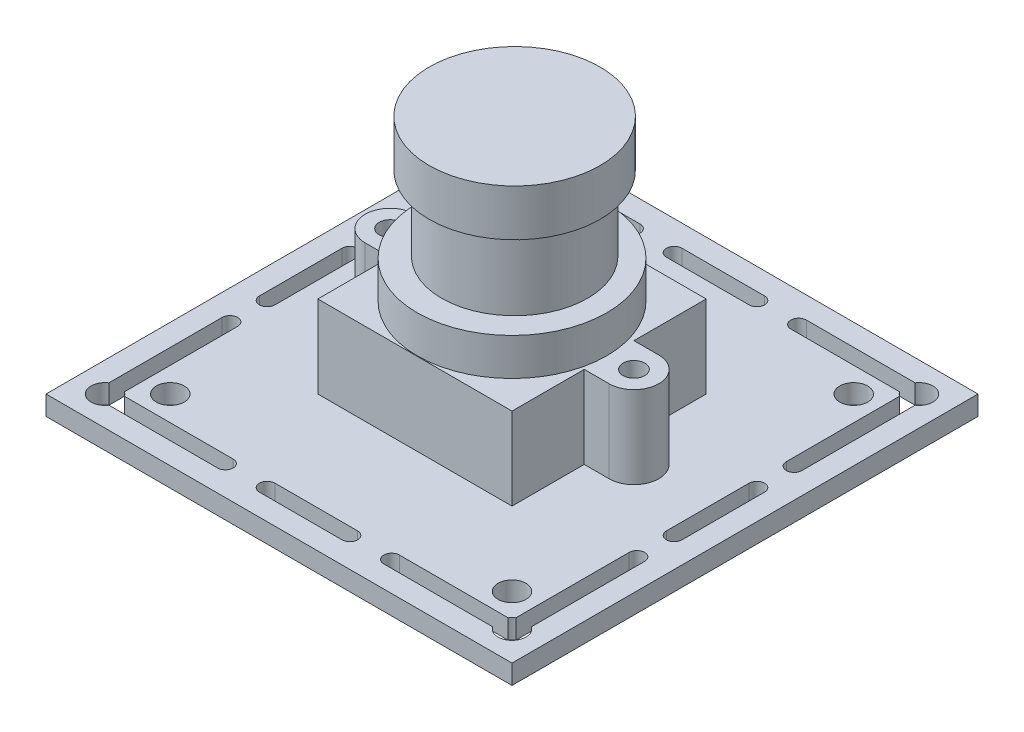
SolidWorks part; units mm, degrees
ref_plane "Front Plane" through (0, 0, 0) normal (0, 0, 1) x (1, 0, 0)
ref_plane "Top Plane" through (0, 0, 0) normal (0, 1, 0) x (1, 0, 0)
ref_plane "Right Plane" through (0, 0, 0) normal (1, 0, 0) x (0, 0, -1)
sketch "Sketch1" plane through (0, 0, 0) normal (0, 1, 0) x (1, 0, 0)
  line L1 (-271.6418, -296.6232) -> (-233.5418, -296.6232)
  line L2 (-271.6418, -296.6232) -> (-271.6418, -334.7232)
  line L3 (-271.6418, -334.7232) -> (-233.5418, -334.7232)
  line L4 (-233.5418, -296.6232) -> (-233.5418, -334.7232)
  line L5 (-271.6418, -296.6232) -> (-233.5418, -334.7232) construction
  line L6 (-271.6418, -334.7232) -> (-233.5418, -296.6232) construction
  point P0 (-252.5918, -315.6732)
  dimension "D1" = 38.1
  dimension "D2" = 38.1
extrude "Boss-Extrude1" add sketch "Sketch1" along normal blind 1.5875
sketch "Sketch4" plane through (0, 1.5875, 0) normal (0, 1, 0) x (1, 0, 0)
  line L0 (-271.6418, -334.7232) -> (-233.5418, -296.6232) construction
  line L1 (-252.5918, -296.6232) -> (-252.5918, -334.7232) construction
  line L2 (-269.2288, -332.3102) -> (-235.9548, -332.3102) construction
  line L3 (-269.2288, -332.3102) -> (-269.2288, -299.0362) construction
  line L4 (-269.8638, -312.295) -> (-269.8638, -319.0514)
  line L5 (-235.9548, -332.3102) -> (-235.9548, -299.0362) construction
  line L6 (-269.2288, -332.3102) -> (-235.9548, -299.0362) construction
  line L7 (-268.4206, -299.8444) -> (-235.9548, -332.3102) construction
  line L8 (-233.5418, -296.6232) -> (-271.6418, -296.6232) construction
  line L9 (-271.6418, -334.7232) -> (-233.5418, -334.7232) construction
  line L10 (-271.6418, -315.6732) -> (-233.5418, -315.6732) construction
  line L11 (-271.6418, -296.6232) -> (-271.6418, -334.7232) construction
  line L12 (-233.5418, -334.7232) -> (-233.5418, -296.6232) construction
  line L13 (-259.3853, -298.4012) -> (-268.2784, -298.4012)
  line L14 (-259.3853, -299.6712) -> (-268.2784, -299.6712)
  line L15 (-255.97, -298.4012) -> (-249.2136, -298.4012)
  line L16 (-255.97, -299.6712) -> (-249.2136, -299.6712)
  line L17 (-255.335, -299.0362) -> (-235.9548, -299.0362) construction
  line L18 (-258.7503, -299.0362) -> (-256.605, -299.0362) construction
  line L19 (-268.5938, -312.295) -> (-268.5938, -319.0514)
  line L20 (-269.2288, -299.6712) -> (-269.2288, -299.0362) construction
  line L21 (-269.8638, -309.247) -> (-269.8638, -299.9865)
  line L22 (-268.5938, -309.247) -> (-268.5938, -299.9865)
  line L23 (-269.2288, -311.66) -> (-269.2288, -309.882) construction
  line L24 (-235.9548, -311.66) -> (-235.9548, -309.882) construction
  line L25 (-235.9548, -299.6712) -> (-235.9548, -299.0362) construction
  line L26 (-246.4333, -299.0362) -> (-248.5786, -299.0362) construction
  line L27 (-236.5898, -309.247) -> (-236.5898, -299.9865)
  line L28 (-235.3198, -309.247) -> (-235.3198, -299.9865)
  line L29 (-236.5898, -312.295) -> (-236.5898, -319.0514)
  line L30 (-245.7983, -299.6712) -> (-236.9052, -299.6712)
  line L31 (-245.7983, -298.4012) -> (-236.9052, -298.4012)
  line L32 (-235.3198, -312.295) -> (-235.3198, -319.0514)
  line L33 (-246.4333, -332.3102) -> (-248.5786, -332.3102) construction
  line L34 (-235.9548, -331.6752) -> (-235.9548, -332.3102) construction
  line L35 (-235.9548, -319.6864) -> (-235.9548, -321.4644) construction
  line L36 (-269.2288, -319.6864) -> (-269.2288, -321.4644) construction
  line L37 (-269.2288, -331.6752) -> (-269.2288, -332.3102) construction
  line L38 (-258.7503, -332.3102) -> (-256.605, -332.3102) construction
  line L39 (-255.335, -332.3102) -> (-235.9548, -332.3102) construction
  line L40 (-268.4206, -331.5019) -> (-235.9548, -299.0362) construction
  line L41 (-269.2288, -299.0362) -> (-235.9548, -332.3102) construction
  line L42 (-271.6418, -296.6232) -> (-233.5418, -334.7232) construction
  line L43 (-245.7983, -332.9452) -> (-236.9052, -332.9452)
  line L44 (-245.7983, -331.6752) -> (-236.9052, -331.6752)
  line L45 (-235.3198, -322.0994) -> (-235.3198, -331.3598)
  line L46 (-236.5898, -322.0994) -> (-236.5898, -331.3598)
  line L47 (-268.5938, -322.0994) -> (-268.5938, -331.3598)
  line L48 (-269.8638, -322.0994) -> (-269.8638, -331.3598)
  line L49 (-255.97, -331.6752) -> (-249.2136, -331.6752)
  line L50 (-255.97, -332.9452) -> (-249.2136, -332.9452)
  line L51 (-259.3853, -331.6752) -> (-268.2784, -331.6752)
  line L52 (-259.3853, -332.9452) -> (-268.2784, -332.9452)
  line L54 (-266.5618, -329.6432) -> (-238.6218, -329.6432) construction
  line L55 (-266.5618, -329.6432) -> (-266.5618, -301.7032) construction
  line L56 (-266.5618, -301.7032) -> (-238.6218, -301.7032) construction
  line L57 (-238.6218, -329.6432) -> (-238.6218, -301.7032) construction
  line L58 (-266.5618, -329.6432) -> (-238.6218, -301.7032) construction
  line L59 (-266.5618, -301.7032) -> (-238.6218, -329.6432) construction
  arc A0 (-255.97, -298.4012) -> (-255.97, -299.6712) centre (-255.97, -299.0362) ccw
  arc A1 (-259.3853, -299.6712) -> (-259.3853, -298.4012) centre (-259.3853, -299.0362) ccw
  arc A2 (-268.2784, -298.4012) -> (-269.8638, -299.9865) centre (-269.2288, -299.0362) ccw
  arc A3 (-268.5938, -312.295) -> (-269.8638, -312.295) centre (-269.2288, -312.295) ccw
  arc A4 (-269.8638, -309.247) -> (-268.5938, -309.247) centre (-269.2288, -309.247) ccw
  arc A5 (-268.5938, -299.9865) -> (-268.2784, -299.6712) centre (-269.2288, -299.0362) ccw
  arc A6 (-236.5898, -299.9865) -> (-236.9052, -299.6712) centre (-235.9548, -299.0362) cw
  arc A7 (-235.3198, -309.247) -> (-236.5898, -309.247) centre (-235.9548, -309.247) cw
  arc A8 (-236.5898, -312.295) -> (-235.3198, -312.295) centre (-235.9548, -312.295) cw
  arc A9 (-236.9052, -298.4012) -> (-235.3198, -299.9865) centre (-235.9548, -299.0362) cw
  arc A10 (-245.7983, -299.6712) -> (-245.7983, -298.4012) centre (-245.7983, -299.0362) cw
  arc A11 (-249.2136, -298.4012) -> (-249.2136, -299.6712) centre (-249.2136, -299.0362) cw
  arc A12 (-249.2136, -332.9452) -> (-249.2136, -331.6752) centre (-249.2136, -332.3102) ccw
  arc A13 (-245.7983, -331.6752) -> (-245.7983, -332.9452) centre (-245.7983, -332.3102) ccw
  arc A14 (-236.9052, -332.9452) -> (-235.3198, -331.3598) centre (-235.9548, -332.3102) ccw
  arc A15 (-236.5898, -319.0514) -> (-235.3198, -319.0514) centre (-235.9548, -319.0514) ccw
  arc A16 (-235.3198, -322.0994) -> (-236.5898, -322.0994) centre (-235.9548, -322.0994) ccw
  arc A17 (-236.5898, -331.3598) -> (-236.9052, -331.6752) centre (-235.9548, -332.3102) ccw
  arc A18 (-268.5938, -331.3598) -> (-268.2784, -331.6752) centre (-269.2288, -332.3102) cw
  arc A19 (-269.8638, -322.0994) -> (-268.5938, -322.0994) centre (-269.2288, -322.0994) cw
  arc A20 (-268.5938, -319.0514) -> (-269.8638, -319.0514) centre (-269.2288, -319.0514) cw
  arc A21 (-268.2784, -332.9452) -> (-269.8638, -331.3598) centre (-269.2288, -332.3102) cw
  arc A22 (-259.3853, -331.6752) -> (-259.3853, -332.9452) centre (-259.3853, -332.3102) cw
  arc A23 (-255.97, -332.9452) -> (-255.97, -331.6752) centre (-255.97, -332.3102) cw
  circle A24 centre (-266.5618, -301.7032) radius 1.143
  circle A25 centre (-238.6218, -301.7032) radius 1.143
  circle A26 centre (-266.5618, -329.6432) radius 1.143
  circle A27 centre (-238.6218, -329.6432) radius 1.143
  point P4 (-252.5918, -315.6732)
  point P31 (-252.5918, -298.4012)
  point P34 (-236.5898, -315.6732)
  point P42 (-252.5918, -331.6752)
  point P44 (-269.8638, -315.6732)
  point P70 (-268.5938, -315.6732)
  point P71 (-252.5918, -299.6712)
  point P84 (-269.2288, -315.6732)
  point P118 (-235.3198, -315.6732)
  point P119 (-252.5918, -332.9452)
  point P120 (-252.5918, -315.6732)
  dimension "D3" = 1.27
  dimension "D4" = 3.3782
  dimension "D5" = 2.286
  dimension "D7" = 3.3782
  dimension "D8" = 1.27
  dimension "D9" = 3.048
  dimension "D12" = 2.286
  dimension "D1" = 33.274
  dimension "D2" = 33.274
  dimension "D6" = 8.8931
  dimension "D10" = 27.94
  dimension "D11" = 27.94
extrude "Cut-Extrude2" cut sketch "Sketch4" against normal blind 7.874
sketch "Sketch6" plane through (0, 1.5875, 0) normal (0, 1, 0) x (1, 0, 0)
  line L0 (-271.6418, -296.6232) -> (-233.5418, -334.7232) construction
  line L2 (-260.5293, -323.6107) -> (-244.6543, -323.6107)
  line L3 (-260.5293, -323.6107) -> (-260.5293, -307.7357)
  line L4 (-260.5293, -307.7357) -> (-244.6543, -307.7357)
  line L5 (-244.6543, -323.6107) -> (-244.6543, -307.7357)
  line L6 (-260.5293, -323.6107) -> (-244.6543, -307.7357) construction
  line L7 (-260.5293, -307.7357) -> (-244.6543, -323.6107) construction
  point P4 (-252.5918, -315.6732)
  dimension "D1" = 15.875
extrude "Boss-Extrude2" add sketch "Sketch6" along normal blind 6.731
sketch "Sketch7" plane through (0, 1.5875, 0) normal (0, 1, 0) x (1, 0, 0)
  line L0 (-242.6223, -313.6412) -> (-244.6543, -313.6412)
  line L1 (-244.6543, -313.6412) -> (-244.6543, -317.7052)
  line L2 (-244.6543, -323.6107) -> (-244.6543, -307.7357) construction
  line L3 (-242.6223, -317.7052) -> (-244.6543, -317.7052)
  line L4 (-252.5918, -296.6232) -> (-252.5918, -334.7232) construction
  line L5 (-233.5418, -296.6232) -> (-271.6418, -296.6232) construction
  line L6 (-271.6418, -334.7232) -> (-233.5418, -334.7232) construction
  line L7 (-262.5613, -317.7052) -> (-260.5293, -317.7052)
  line L8 (-260.5293, -313.6412) -> (-260.5293, -317.7052)
  line L9 (-262.5613, -313.6412) -> (-260.5293, -313.6412)
  arc A0 (-242.6223, -317.7052) -> (-242.6223, -313.6412) centre (-242.6223, -315.6732) ccw
  circle A1 centre (-242.6223, -315.6732) radius 0.889
  circle A2 centre (-262.5613, -315.6732) radius 0.889
  arc A3 (-262.5613, -317.7052) -> (-262.5613, -313.6412) centre (-262.5613, -315.6732) cw
  dimension "D3" = 4.064
  dimension "D1" = 1.778
extrude "Boss-Extrude3" add sketch "Sketch7" along normal blind 6.731
sketch "Sketch8" plane through (0, 8.3185, 0) normal (0, 1, 0) x (1, 0, 0)
  line L0 (-260.5293, -307.7357) -> (-244.6543, -323.6107) construction
  line L1 (-244.6543, -307.7357) -> (-260.5293, -307.7357) construction
  circle A0 centre (-252.4364, -315.8286) radius 7.747
  dimension "D1" = 15.494
extrude "Boss-Extrude4" add sketch "Sketch8" along normal blind 3.048
sketch "Sketch9" plane through (0, 11.3665, 0) normal (0, 1, 0) x (1, 0, 0)
  circle A0 centre (-252.4654, -315.5831) radius 5.969
  dimension "D1" = 11.938
extrude "Boss-Extrude5" add sketch "Sketch9" along normal blind 6.096
sketch "Sketch10" plane through (0, 17.4625, 0) normal (0, 1, 0) x (1, 0, 0)
  circle A0 centre (-252.4654, -315.5831) radius 6.985
  dimension "D1" = 13.97
extrude "Boss-Extrude6" add sketch "Sketch10" along normal blind 3.81
sketch "Sketch11" plane through (0, 0, 0) normal (0, -1, 0) x (1, 0, 0)
  line L0 (-268.2784, 299.6712) -> (-259.3853, 299.6712) construction
  line L1 (-261.6904, 299.6712) -> (-251.7844, 299.6712)
  line L2 (-261.6904, 299.6712) -> (-261.6904, 304.2432)
  line L3 (-261.6904, 304.2432) -> (-251.7844, 304.2432)
  line L4 (-251.7844, 299.6712) -> (-251.7844, 304.2432)
  dimension "D1" = 9.906
  dimension "D2" = 4.572
extrude "Boss-Extrude7" add sketch "Sketch11" along normal blind 8.255
